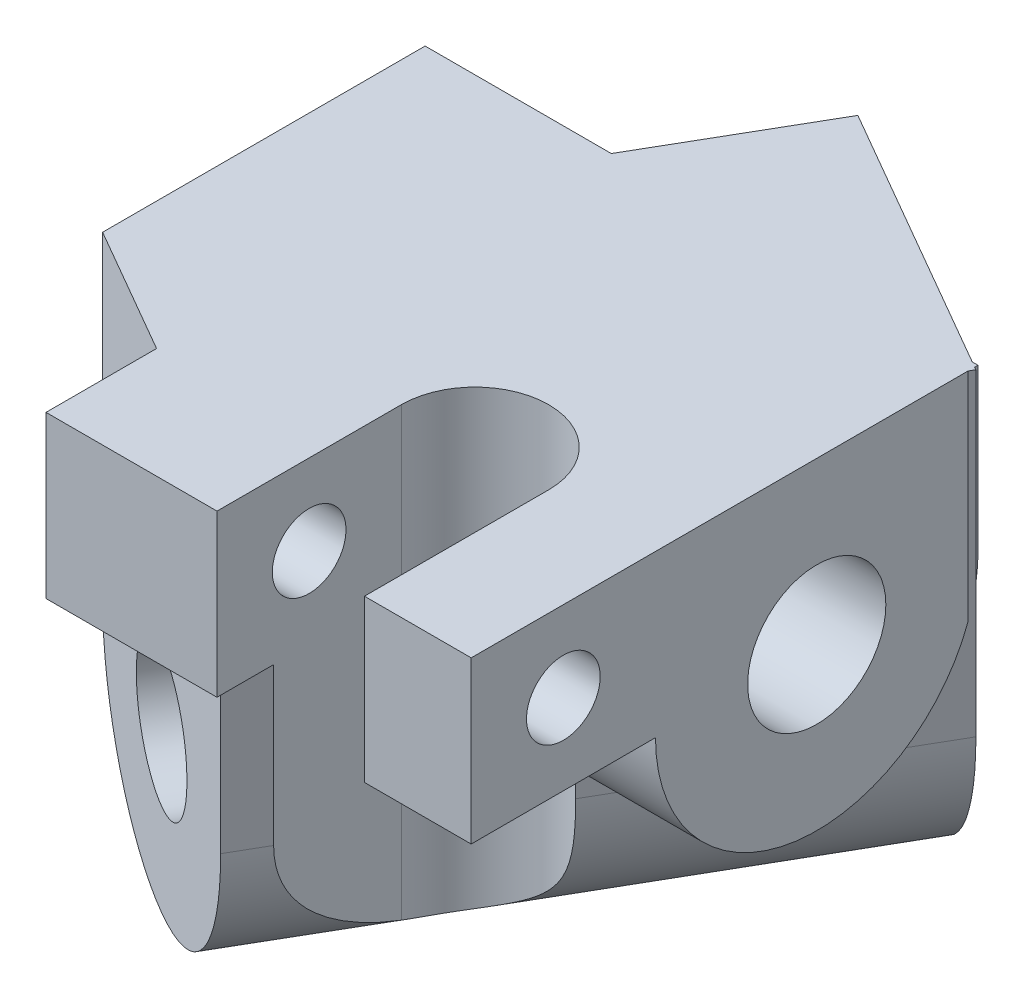
SolidWorks part; units mm, degrees
ref_plane "Front Plane" through (0, 0, 0) normal (0, 0, 1) x (1, 0, 0)
ref_plane "Top Plane" through (0, 0, 0) normal (0, 1, 0) x (1, 0, 0)
ref_plane "Right Plane" through (0, 0, 0) normal (1, 0, 0) x (0, 0, -1)
sketch "Sketch1" plane through (0, 0, 0) normal (1, 0, 0) x (0, 0, -1)
  line L0 (-8.75, 0) -> (8.75, 0)
  line L1 (8.75, 0) -> (8.75, 8.75)
  line L2 (-8.75, 8.75) -> (-8.75, 0)
  arc A0 (8.75, 8.75) -> (-8.75, 8.75) centre (0, 8.75) ccw
  circle A1 centre (0, 8.75) radius 3.75
  dimension "D1" = 8.75
  dimension "D3" = 7.5
  dimension "D2" = 5
extrude "Boss-Extrude1" add sketch "Sketch1" along normal blind 30
ref_plane "Plane1" through (-3.7889, 0, 6.5625) normal (0.5, 0, -0.866) x (-0.866, 0, -0.5)
sketch "Sketch2" plane through (-3.7889, 0, 6.5625) normal (0.5, 0, -0.866) x (-0.866, 0, -0.5)
  line L0 (-4.375, 0) -> (-4.375, 17.25)
  line L1 (-21.875, 17.25) -> (-21.875, 0)
  line L2 (-30.3558, 0) -> (-4.375, 0) construction
  line L3 (-21.875, 0) -> (-4.375, 0)
  line L4 (0, 12.5) -> (-31.5247, 12.5) construction
  arc A0 (-4.375, 17.25) -> (-21.875, 17.25) centre (-13.125, 17.25) ccw
  circle A1 centre (-13.125, 17.25) radius 3.75
  ellipse E0 centre (0, 8.75) end of major axis (0, 12.5) minor radius 1.875 construction
  ellipse E1 centre (0, 8.75) end of major axis (0, 12.5) minor radius 1.875 construction
  dimension "D1" = 8.75
  dimension "D2" = 7.5
  dimension "D3" = 1
extrude "Boss-Extrude2" add sketch "Sketch2" along normal blind 30
sketch "Sketch3" plane through (0, 0, 0) normal (0, -1, 0) x (1, 0, 0)
  line L1 (17.3205, 3.75) -> (10.8253, 15) construction
  line L3 (20.2073, 8.75) -> (15.1554, 17.5) construction
  line L4 (17.3205, 3.75) -> (30, 3.75) construction
  line L5 (30, 8.75) -> (30, -8.2115) construction
  line L6 (30, 8.75) -> (20.2073, 8.75) construction
  line L7 (-7.9566, 4.1562) -> (0.3789, 8.9687) construction
  line L8 (24.2073, 8.75) -> (24.2073, 15.6782)
  line L9 (16.2073, 15.6782) -> (24.2073, 15.6782)
  line L10 (16.2073, 15.6782) -> (16.2073, 8.75)
  arc A0 (16.2073, 8.75) -> (24.2073, 8.75) centre (20.2073, 8.75) ccw
  dimension "D1" = 8
  dimension "D2" = 5
  dimension "D3" = 5
extrude "Cut-Extrude1" cut sketch "Sketch3" against normal through all
sketch "Sketch4" plane through (0, 0, 0) normal (0, -1, 0) x (1, 0, 0)
  line L0 (24.2073, 8.75) -> (24.2073, 18.75)
  line L1 (24.2073, 18.75) -> (30, 18.75)
  line L2 (30, 18.75) -> (30, 8.75)
  line L3 (30, 8.75) -> (24.2073, 8.75)
  arc A0 (16.2073, 8.75) -> (24.2073, 8.75) centre (20.2073, 8.75) ccw construction
  arc A1 (16.2073, 8.75) -> (24.2073, 8.75) centre (20.2073, 8.75) ccw construction
  circle A2 centre (20.2073, 8.75) radius 4 construction
  dimension "D1" = 6
extrude "Boss-Extrude3" add sketch "Sketch4" against normal blind 8.75
sketch "Sketch6" plane through (0, 0, 0) normal (0, -1, 0) x (1, 0, 0)
  line L0 (16.2073, 15.6782) -> (16.2073, 18.75)
  line L1 (16.2073, 18.75) -> (6.9282, 18.75)
  line L2 (6.9282, 18.75) -> (6.9282, 12.75)
  line L3 (15.1554, 17.5) -> (0, 8.75) construction
  line L4 (30, 18.75) -> (24.2073, 18.75) construction
  line L5 (6.9282, 12.75) -> (16.2073, 15.6782)
  dimension "D1" = 6
extrude "Boss-Extrude4" add sketch "Sketch6" against normal up to surface (8.75 mm away) up to face at (27.1036, 8.75, 13.75)
sketch "Sketch5" plane through (30, 0, 0) normal (1, 0, 0) x (0, 0, -1)
  line L0 (-14.9644, 4.375) -> (-9.1409, 4.375) construction
  line L1 (-8.75, 8.75) -> (-18.75, 8.75) construction
  line L3 (-15.3741, 8.75) -> (-10.3407, 8.75) construction
  line L4 (-14.9644, 0) -> (-9.931, 0) construction
  line L5 (-18.75, 0) -> (8.2115, 0) construction
  line L6 (-18.75, 8.75) -> (-18.75, 0) construction
  circle A0 centre (-13.75, 4.375) radius 2
  dimension "D1" = 4
  dimension "D2" = 5
extrude "Cut-Extrude2" cut sketch "Sketch5" against normal through all
sketch "Sketch7" plane through (0, 0, 0) normal (-1, 0, 0) x (0, 0, 1)
  circle A0 centre (0, 8.75) radius 3.75 construction
  circle A1 centre (0, 8.75) radius 3.75
extrude "Cut-Extrude3" cut sketch "Sketch7" against normal through all
sketch "Sketch8" plane through (-3.7889, 0, 6.5625) normal (-0.5, 0, 0.866) x (0.866, 0, 0.5)
  circle A0 centre (13.125, 17.25) radius 3.75 construction
  circle A1 centre (13.125, 17.25) radius 3.75
extrude "Cut-Extrude4" cut sketch "Sketch8" against normal through all
mirror "Mirror1" about plane through (30, 0, 8.75) normal (0, 1, 0) of bodies 108
delete or keep bodies "Body-Delete1" type delete bodies bodies 108
